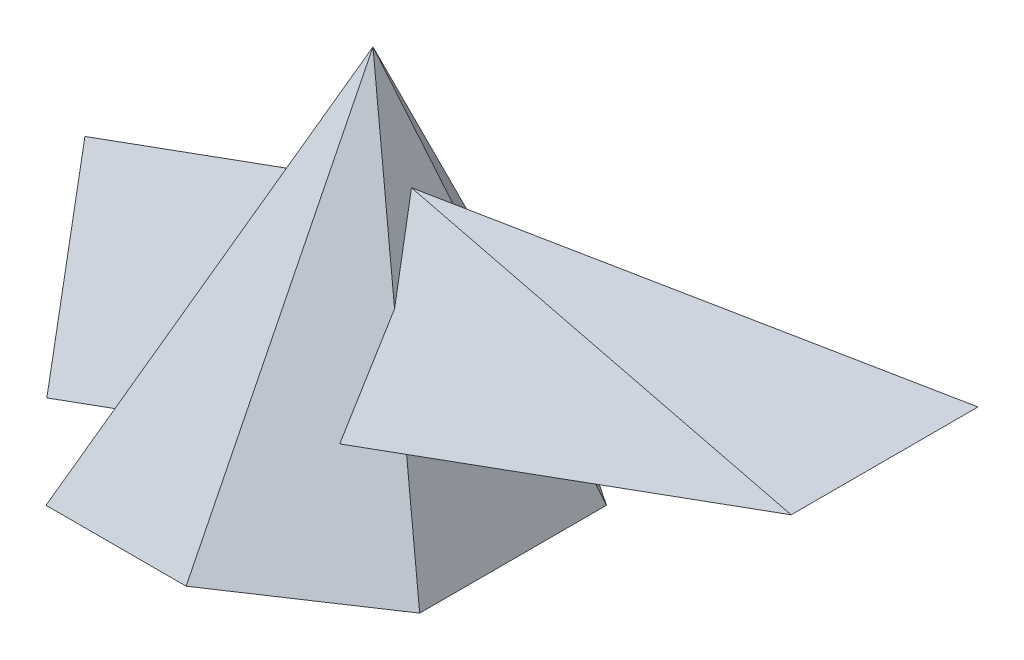
SolidWorks part; units mm, degrees
ref_plane "Front Plane" through (0, 0, 0) normal (0, 0, 1) x (1, 0, 0)
ref_plane "Top Plane" through (0, 0, 0) normal (0, 1, 0) x (1, 0, 0)
ref_plane "Right Plane" through (0, 0, 0) normal (1, 0, 0) x (0, 0, -1)
sketch "Base" plane through (0, 0, 0) normal (0, 1, 0) x (1, 0, 0)
  line L0 (0, 40) -> (0, -40)
  line L1 (0, -40) -> (30, -40)
  line L2 (30, -40) -> (60, -20)
  line L3 (60, -20) -> (60, 20)
  line L4 (60, 20) -> (30, 40)
  line L5 (30, 40) -> (0, 40)
  dimension "D1" = 80
  dimension "D2" = 30
  dimension "D3" = 40
  dimension "D4" = 30
  dimension "D5" = 20
ref_plane "Plane for apex of pyramid" through (0, 80, 0) normal (0, 1, 0) x (1, 0, 0)
sketch "Apex" plane through (0, 80, 0) normal (0, 1, 0) x (1, 0, 0)
  point P0 (30, 0)
loft "Loft of pyramid" add profiles "Base", "Apex"
sketch "Point at 22mm" plane through (0, 0, 0) normal (0, 0, 1) x (1, 0, 0)
  line L0 (60, 0) -> (30, 80) construction
  point P0 (38.25, 58)
  dimension "D1" = 22
ref_plane "70 deg plane" through (0, 0, 0) normal (-0.9397, -0.342, 0) x (-0.342, 0.9397, 0)
ref_plane "70 deg at point" through (52.4164, 19.078, 0) normal (-0.9397, -0.342, 0) x (0, 0, 1)
sketch "40mm triangle" plane through (52.4164, 19.078, 0) normal (-0.9397, -0.342, 0) x (0, 0, 1)
  line L0 (0, 41.4199) -> (20, 6.7789)
  line L1 (20, 6.7789) -> (-20, 6.7789)
  line L2 (-20, 6.7789) -> (0, 41.4199)
  dimension "D1" = 40
extrude "Triangular Prism" add sketch "40mm triangle" along normal blind 100 and the other way blind 100
sketch "Sketch6" plane through (0, 0, 0) normal (0, 0, 1) x (1, 0, 0)
  line L0 (-19.8201, 0) -> (-43.8713, -8.7539)
  line L1 (3.1328, 8.3542) -> (-43.8713, -8.7539) construction
  line L2 (-43.8713, -8.7539) -> (-55.7193, 23.798)
  line L3 (-55.7193, 23.798) -> (-31.6681, 32.5519)
  line L4 (19.142, 51.0452) -> (-55.7193, 23.798) construction
  line L5 (-31.6681, 32.5519) -> (-19.8201, 0)
extrude "LHS cut" cut sketch "Sketch6" against normal through all and the other way through all
sketch "Sketch7" plane through (0, 0, 0) normal (0, 0, 1) x (1, 0, 0)
  line L0 (38.25, 58) -> (139.5336, 58)
  line L1 (144.0672, 59.6501) -> (42.8833, 22.8222) construction
  line L2 (38.25, 58) -> (132.2193, 92.202)
  line L3 (132.2193, 92.202) -> (144.0672, 59.6501)
  line L4 (144.0672, 59.6501) -> (139.5336, 58)
extrude "RHS cut" cut sketch "Sketch7" against normal through all and the other way through all
